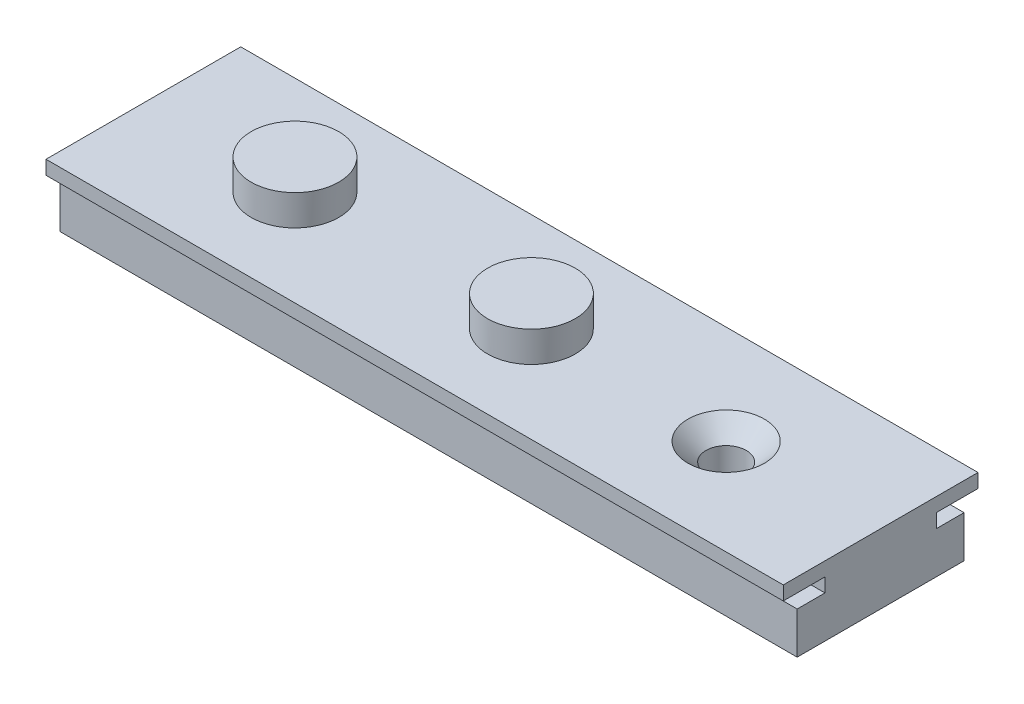
SolidWorks part; units mm, degrees
ref_plane "Front Plane" through (0, 0, 0) normal (0, 0, 1) x (1, 0, 0)
ref_plane "Top Plane" through (0, 0, 0) normal (0, 1, 0) x (1, 0, 0)
ref_plane "Right Plane" through (0, 0, 0) normal (1, 0, 0) x (0, 0, -1)
sketch "Sketch1" plane through (0, 0, 0) normal (1, 0, 0) x (0, 0, -1)
  line L0 (-125.8954, 0) -> (125.8954, 0) construction
  line L1 (0, 98.3558) -> (0, -98.3558) construction
  line L2 (4, 0.5) -> (6, 0.5)
  line L3 (6, 0.5) -> (6, -2.5)
  line L4 (6, -2.5) -> (-6, -2.5)
  line L5 (-6, -2.5) -> (-6, 0.5)
  line L6 (-6, 0.5) -> (-4, 0.5)
  line L7 (-4, 0.5) -> (-4, 1.5)
  line L8 (-7, 1.5) -> (-7, 2.5)
  line L9 (-4, 1.5) -> (-7, 1.5)
  line L10 (4, 0.5) -> (4, 1.5)
  line L11 (4, 1.5) -> (7, 1.5)
  line L12 (7, 1.5) -> (7, 2.5)
  line L13 (7, 2.5) -> (-7, 2.5)
  point P0 (0, 0)
  point P4 (0, 0)
  point P8 (0, 0)
  dimension "D1" = 1
  dimension "D2" = 5
  dimension "D3" = 14
  dimension "D4" = 1
  dimension "D5" = 3
  dimension "D6" = 12
  dimension "D7" = 7
  dimension "D8" = 2.5
  dimension "D9" = 1
  dimension "D10" = 3
  dimension "D11" = 6
  dimension "D12" = 0.5
extrude "Boss-Extrude1" add sketch "Sketch1" along normal blind 53
sketch "Sketch2" plane through (0, 2.5, 0) normal (0, 1, 0) x (1, 0, 0)
  line L0 (-11.5061, -0.104) -> (64.5061, -0.104) construction
  line L1 (26.5, 19.8776) -> (26.5, -20.0856) construction
  line L2 (0, 7) -> (0, -7) construction
  line L7 (53, 7) -> (53, -7) construction
  arc A0 (44.2725, -0.104) -> (39.7275, -0.104) centre (42, -0.104) ccw
  arc A1 (39.7275, -0.104) -> (44.2725, -0.104) centre (42, -0.104) ccw
  arc A2 (14.15, -0.104) -> (7.85, -0.104) centre (11, -0.104) ccw
  arc A3 (7.85, -0.104) -> (14.15, -0.104) centre (11, -0.104) ccw
  arc A4 (31.15, -0.104) -> (24.85, -0.104) centre (28, -0.104) ccw
  arc A5 (24.85, -0.104) -> (31.15, -0.104) centre (28, -0.104) ccw
  point P3 (26.5, -0.104)
  point P6 (26.5, -0.104)
  point P9 (25.3067, -1.6744)
  point P10 (25.3067, -1.6744)
  point P14 (0, 0)
  dimension "D5" = 3.15
  dimension "D6" = 3.15
  dimension "D7" = 2.2725
  dimension "D1" = 26.5
  dimension "D2" = 11
  dimension "D3" = 14
  dimension "D4" = 17
hole_wizard "CSK for M2.5 Countersunk Flat Head Screw1" positions "3DSketch1" profile "Sketch5" countersink size "M2.5" standard "ISO"
sketch3d "3DSketch1"
  point P0 (42, 2.5, 0.104)
sketch "Sketch5" plane through (42, 2.5, 0.104) normal (1, 0, 0) x (0, 0, 1)
  line L0 (0, 0) -> (0, 14.8712)
  line L1 (0, 14.8712) -> (1.45, 14)
  line L2 (1.45, 14) -> (1.45, 1.3)
  line L3 (1.45, 1.3) -> (2.75, 0)
  line L5 (2.75, 0) -> (0, 0)
  line L6 (-1.45, 1.3) -> (-2.75, 0) construction
  line L10 (0, 14.8712) -> (-1.45, 14) construction
  line L11 (0, -6.35) -> (0, 107.95) construction
  dimension "Hole Dia." = 2.9
  dimension "Hole Depth" = 14
  dimension "Near C'Sink Dia." = 5.5
  dimension "Near C'Sink Angle" = 90
  dimension "Drill Angle" = 118
extrude "Boss-Extrude2" add sketch "Sketch2" along normal blind 2.2 contours A2 A3 | A4 A5
